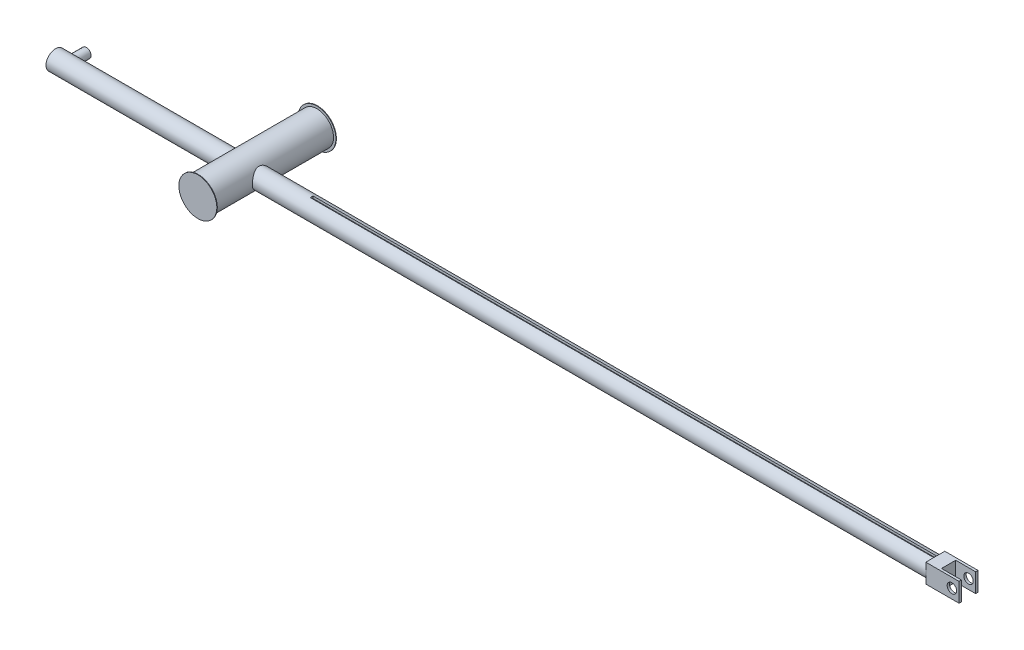
SolidWorks part; units mm, degrees
material "普通碳钢"
ref_plane "前视基准面" through (0, 0, 0) normal (0, 0, 1) x (1, 0, 0)
ref_plane "上视基准面" through (0, 0, 0) normal (0, 1, 0) x (1, 0, 0)
ref_plane "右视基准面" through (0, 0, 0) normal (1, 0, 0) x (0, 0, -1)
sketch "草图1" plane through (0, 0, 0) normal (1, 0, 0) x (0, 0, -1)
  circle A0 centre (0, 0) radius 2
  dimension "D1" = 4
extrude "凸台-拉伸1" add sketch "草图1" along normal blind 192.4
sketch "草图2" plane through (0, 0, 0) normal (0, 0, 1) x (1, 0, 0)
  line L0 (192.4, 0) -> (0, 0) construction
  circle A0 centre (2, 0) radius 1
  dimension "D1" = 2
  dimension "D2" = 2
extrude "凸台-拉伸2" add sketch "草图2" against normal blind 4.5
sketch "草图3" plane through (0, 0, 0) normal (0, 0, 1) x (1, 0, 0)
  circle A0 centre (40, 0) radius 3.5
  dimension "D1" = 7
  dimension "D2" = 40
extrude "凸台-拉伸3" add sketch "草图3" along normal blind 10 and the other way blind 15.1
sketch "草图4" plane through (0, 0, 10) normal (0, 0, 1) x (1, 0, 0)
  circle A0 centre (40, 0) radius 4
  dimension "D1" = 8
extrude "凸台-拉伸4" add sketch "草图4" against normal blind 0.1
sketch "草图5" plane through (0, 0, -15.1) normal (0, 0, -1) x (-1, 0, 0)
  circle A1 centre (-40, 0) radius 4
  circle A2 centre (-40, 0) radius 4
  dimension "D1" = 0
extrude "凸台-拉伸5" add sketch "草图5" along normal blind 0.1
sketch "草图6" plane through (0, 0, 0) normal (0, 1, 0) x (1, 0, 0)
  line L0 (43.5, -2) -> (192.4, -2) construction
  line L1 (192.4, 2) -> (185.4, 2)
  line L2 (192.4, 2) -> (192.4, -2)
  line L3 (192.4, -2) -> (185.4, -2)
  line L4 (185.4, 2) -> (185.4, -2)
  dimension "D1" = 7
extrude "凸台-拉伸6" add sketch "草图6" along normal mid plane 4
sketch "草图7" plane through (0, 0, 0) normal (0, 1, 0) x (1, 0, 0)
  line L0 (192.4, -2) -> (192.4, 2) construction
  line L1 (192.4, 1.5) -> (188.2, 1.5)
  line L2 (192.4, 1.5) -> (192.4, -1.5)
  line L3 (192.4, -1.5) -> (188.2, -1.5)
  line L4 (188.2, 1.5) -> (188.2, -1.5)
  line L5 (185.4, -2) -> (192.4, -2) construction
  dimension "D1" = 3
  dimension "D2" = 0.5
  dimension "D3" = 4.2
extrude "切除-拉伸1" cut sketch "草图7" against normal mid plane 4
sketch "草图8" plane through (0, 0, 0) normal (0, 0, 1) x (1, 0, 0)
  line L0 (192.4, 2) -> (192.4, -2) construction
  line L1 (190.9, 0) -> (192.4, 0) construction
  circle A0 centre (190.9, 0) radius 1
  dimension "D1" = 2
  dimension "D2" = 1.5
extrude "切除-拉伸2" cut sketch "草图8" against normal mid plane 4
sketch "草图9" plane through (0, 2, 0) normal (0, 1, 0) x (1, 0, 0)
  line L0 (185.4, 0) -> (185.4, -2) construction
  line L1 (54, 0.3) -> (185.4, 0.3)
  line L2 (54, 0.3) -> (54, -0.3)
  line L3 (54, -0.3) -> (185.4, -0.3)
  line L4 (185.4, 0.3) -> (185.4, -0.3)
  line L5 (54, 0) -> (0, 0) construction
  dimension "D1" = 0.6
  dimension "D2" = 54
extrude "切除-拉伸3" cut sketch "草图9" against normal blind 0.5
